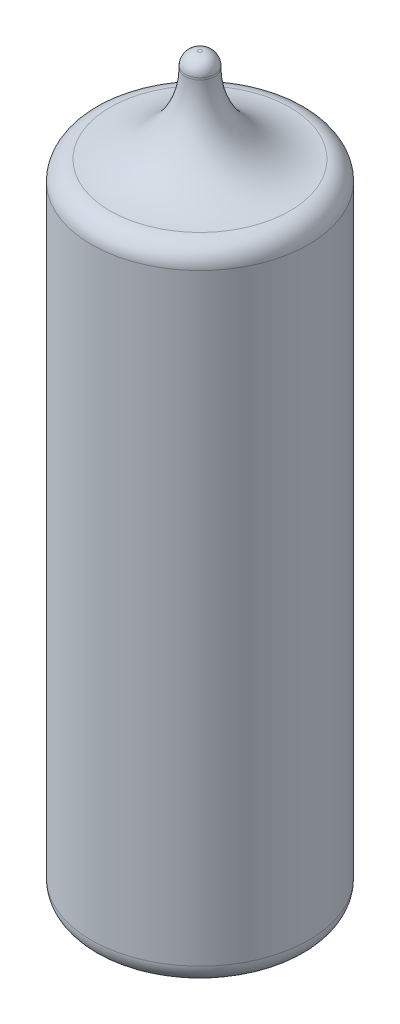
SolidWorks part; units mm, degrees
material "Epoxy, Unfilled"
ref_plane "Front Plane" through (0, 0, 0) normal (0, 0, 1) x (1, 0, 0)
ref_plane "Top Plane" through (0, 0, 0) normal (0, 1, 0) x (1, 0, 0)
ref_plane "Right Plane" through (0, 0, 0) normal (1, 0, 0) x (0, 0, -1)
sketch "Sketch1" plane through (0, 0, 0) normal (0, 1, 0) x (1, 0, 0)
  circle A0 centre (0, 0) radius 11
  dimension "D1" = 22
extrude "Boss-Extrude1" add sketch "Sketch1" along normal blind 65
sketch "Sketch2" plane through (0, 65, 0) normal (0, 1, 0) x (1, 0, 0)
  circle A0 centre (0, 0) radius 1.5
  dimension "D1" = 3
extrude "Boss-Extrude2" add sketch "Sketch2" along normal blind 9.5
fillet "Fillet1" radius 1.3 1 edges at (0, 74.5, 1.5)
fillet "Fillet2" radius 8 1 edges at (0, 65, 1.5)
fillet "Fillet3" radius 2 1 edges at (0, 65, 11)
fillet "Fillet4" radius 2 1 edges at (0, 0, 11)
